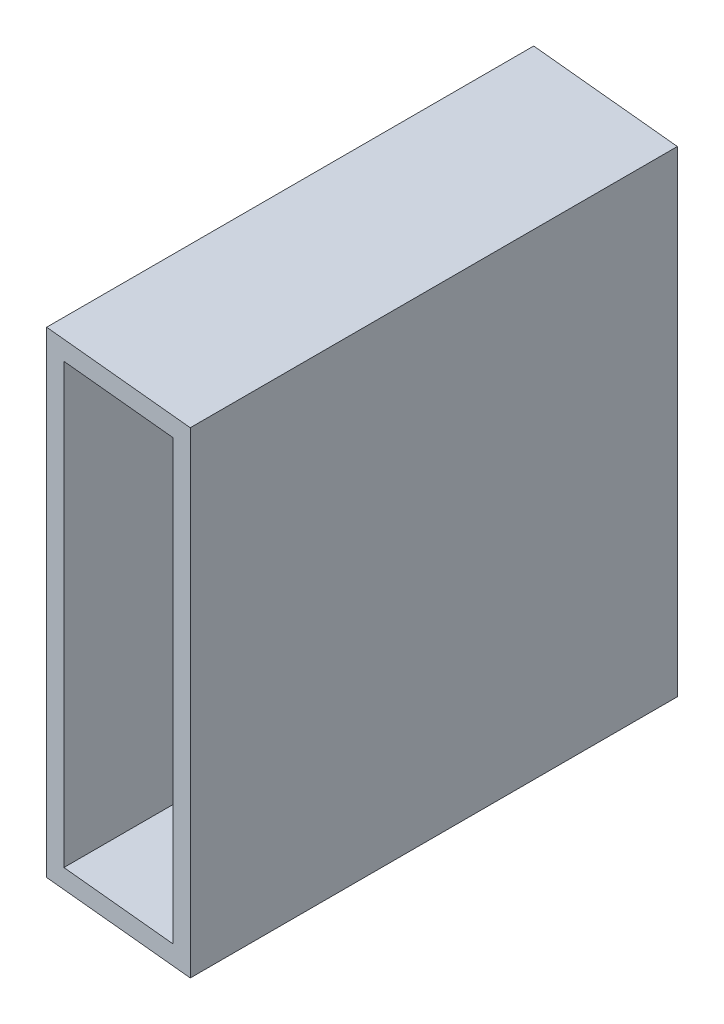
SolidWorks part; units mm, degrees
material "A500"
ref_plane "Front Plane" through (0, 0, 0) normal (0, 0, 1) x (1, 0, 0)
ref_plane "Top Plane" through (0, 0, 0) normal (0, 1, 0) x (1, 0, 0)
ref_plane "Right Plane" through (0, 0, 0) normal (1, 0, 0) x (0, 0, -1)
sketch "Sketch2" plane through (0, 0, 0) normal (0, 0, 1) x (1, 0, 0)
  line L0 (0, 0) -> (0, 38.1)
  line L1 (0, 38.1) -> (12.7, 38.1)
  line L2 (12.7, 38.1) -> (12.7, 0)
  line L3 (12.7, 0) -> (0, 0)
  line L4 (12.7, -38.1) -> (12.7, -35.052)
  line L5 (0, 0) -> (-12.7, 0)
  line L6 (0, 0) -> (0, -38.1)
  line L7 (0, -38.1) -> (-12.7, -38.1)
  line L8 (-12.7, 0) -> (-12.7, -38.1)
  line L9 (-12.7, -38.1) -> (12.7, -38.1)
  line L10 (-12.7, -38.1) -> (-12.7, 38.1)
  line L11 (-12.7, 38.1) -> (12.7, 38.1)
  line L12 (12.7, -38.1) -> (12.7, 38.1)
  line L13 (12.7, -35.052) -> (9.652, -35.052)
  line L14 (-12.7, 38.1) -> (-9.652, 38.1)
  line L15 (-9.652, 38.1) -> (-9.652, 35.052)
  line L17 (-9.652, 35.052) -> (9.652, 35.052)
  line L18 (-9.652, 35.052) -> (-9.652, -35.052)
  line L19 (-9.652, -35.052) -> (9.652, -35.052)
  line L20 (9.652, 35.052) -> (9.652, -35.052)
  dimension "D1" = 38.1
  dimension "D2" = 12.7
  dimension "D3" = 38.1
  dimension "D4" = 12.7
  dimension "D5" = 3.048
  dimension "D6" = 3.048
  dimension "D7" = 3.048
  dimension "D8" = 3.048
extrude "Boss-Extrude1" add sketch "Sketch2" along normal up to vertex (77.8823 mm away) contours L18 L15 L11 L10 L5 | L15 L17 L0 L11 | L17 L20 L3 L2 L1 L0 | L3 L20 L13 L12 | L19 L18 L5 L8 L7 L6 | L19 L6 L9 L4 L13
sketch "Sketch3" plane through (0, 0, 0) normal (0, 0, -1) x (-1, 0, 0)
  line L1 (-12.7, 38.1) -> (12.7, 38.1)
  line L2 (-12.7, 38.1) -> (-12.7, -38.1)
  line L3 (-12.7, -38.1) -> (12.7, -38.1)
  line L4 (12.7, 38.1) -> (12.7, -38.1)
  line L5 (9.652, -35.052) -> (-9.652, -35.052)
  line L6 (9.652, -35.052) -> (9.652, 35.052)
  line L7 (9.652, 35.052) -> (-9.652, 35.052)
  line L8 (-9.652, -35.052) -> (-9.652, 35.052)
extrude "Boss-Extrude2" add sketch "Sketch3" along normal blind 50
sketch "Sketch4" plane through (0, 38.1, 0) normal (0, 1, 0) x (1, 0, 0)
  line L0 (119.7295, -11.4807) -> (-119.7295, 11.4807)
  line L1 (0, -50) -> (0, 0)
  line L2 (0, -77.8823) -> (0, 0) construction
  line L3 (0, 0) -> (9.5015, 49.0889)
  line L4 (65.1804, 336.7499) -> (0, 0) construction
  line L5 (9.5015, 49.0889) -> (-119.7295, 11.4807)
  line L6 (0, -50) -> (-119.7295, 11.4807)
  line L7 (-119.7295, 11.4807) -> (119.7295, -11.4807)
  line L8 (-119.7295, 11.4807) -> (-112.2822, 89.1469)
  line L9 (119.7295, -11.4807) -> (127.1768, 66.1854)
  line L10 (-112.2822, 89.1469) -> (127.1768, 66.1854)
  line M6 (12.7, -77.8823) -> (12.7, 50)
  line M7 (12.7, 50) -> (-12.7, 50)
  line M8 (-12.7, 50) -> (-12.7, -77.8823)
  dimension "D1" = 50
  dimension "D2" = 50
extrude "Cut-Extrude1" cut sketch "Sketch4" against normal through all both and the other way through all contours L5 L0 M8 | L3 L5 L0 M8 | L10 L8 L5 L0 L9 M8 M7 M6 | L5 L3 L0 M6 M7 M8
sketch "Sketch5" plane through (0, 0, 77.8823) normal (0, 0, 1) x (1, 0, 0)
  line L1 (12.7, -38.1) -> (-12.7, -38.1)
  line L2 (12.7, -38.1) -> (12.7, 38.1)
  line L3 (12.7, 38.1) -> (-12.7, 38.1)
  line L4 (-12.7, -38.1) -> (-12.7, 38.1)
  line L5 (9.652, -35.052) -> (-9.652, -35.052)
  line L6 (9.652, -35.052) -> (9.652, 35.052)
  line L7 (9.652, 35.052) -> (-9.652, 35.052)
  line L8 (-9.652, -35.052) -> (-9.652, 35.052)
extrude "Boss-Extrude3" add sketch "Sketch5" along normal blind 50
sketch "Sketch6" plane through (0, -38.1, 0) normal (0, -1, 0) x (1, 0, 0)
  line L0 (-103.7149, 67.9372) -> (103.7149, 87.8274)
  line L1 (0, 27.8823) -> (0, 77.8823)
  line L2 (0, 77.8823) -> (0, 0) construction
  line L3 (-9.5015, 126.9712) -> (0, 77.8823)
  line L4 (-59.8596, 387.1424) -> (0, 77.8823) construction
  line L5 (-9.5015, 126.9712) -> (-103.7149, 67.9372)
  line L6 (0, 27.8823) -> (-103.7149, 67.9372)
  line L7 (-103.7149, 67.9372) -> (103.7149, 87.8274)
  line L8 (-103.7149, 67.9372) -> (-113.1612, 166.4507)
  line L9 (103.7149, 87.8274) -> (94.2685, 186.3409)
  line L10 (-113.1612, 166.4507) -> (94.2685, 186.3409)
  line M1 (-12.7, 127.8823) -> (-12.7, -1.2178)
  line M3 (12.7, 1.2178) -> (12.7, 127.8823)
  line M4 (12.7, 127.8823) -> (-12.7, 127.8823)
  dimension "D1" = 50
  dimension "D2" = 50
extrude "Cut-Extrude2" cut sketch "Sketch6" against normal through all both and the other way through all contours L10 L8 L5 L0 L9 M1 M4 M3 | L5 L0 M1 | L5 L3 L0 M3 M4 M1 | L3 L5 L0 M1
equation "\"D3@Sketch2\"=\"D1@Sketch2\""
equation "\"D4@Sketch2\"=\"D2@Sketch2\""
